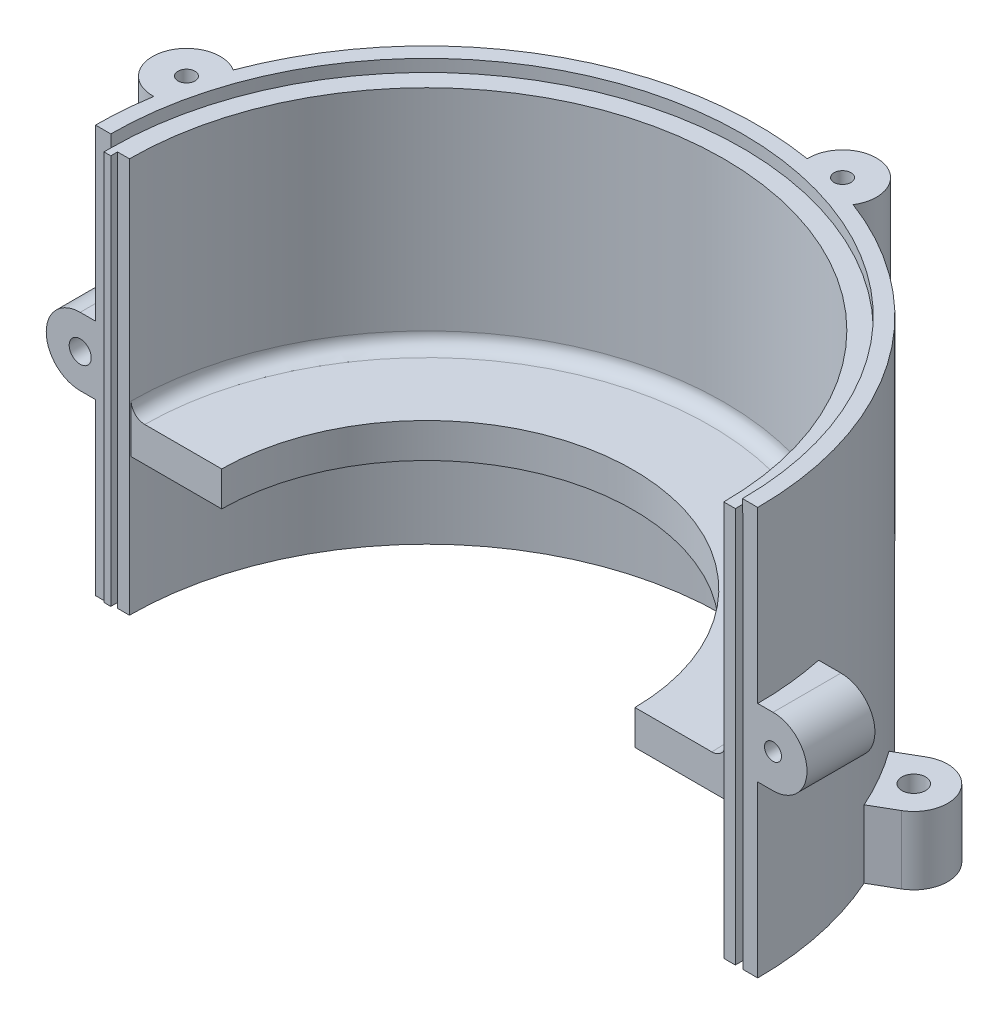
SolidWorks part; units mm, degrees
ref_plane "Plano frontal" through (0, 0, 0) normal (0, 0, 1) x (1, 0, 0)
ref_plane "Plano superior" through (0, 0, 0) normal (0, 1, 0) x (1, 0, 0)
ref_plane "Plano direito" through (0, 0, 0) normal (1, 0, 0) x (0, 0, -1)
sketch "Esboço3" plane through (0, 0, 0) normal (0, 0, 1) x (1, 0, 0)
  line L2 (97.5, 79.8) -> (97.5, 11.3045)
  line L4 (87.5, 0) -> (60.3424, 0)
  line L6 (60.3424, 0) -> (60.3424, 10.2)
  line L18 (97.5, 79.8) -> (93, 79.8)
  line L19 (93, 79.8) -> (93, 76.2)
  line L20 (93, 76.2) -> (87.5, 76.2)
  line L21 (87.5, 76.2) -> (87.5, 14.2)
  line L22 (83.5, 10.2) -> (60.3424, 10.2)
  line L30 (55, 0) -> (-55, 0) construction
  line L33 (97.5, 0) -> (97.5, 11.3045)
  line L34 (97.5, 0) -> (97.5, -40.2)
  line L35 (97.5, -40.2) -> (87.5, -40.2)
  line L36 (87.5, -40.2) -> (87.5, 0)
  arc A1 (87.5, 14.2) -> (83.5, 10.2) centre (83.5, 14.2) cw
  dimension "D32" = 79.8
  dimension "D5" = 120
  dimension "D11" = 66
  dimension "D12" = 3.6
  dimension "D13" = 93
  dimension "D14" = 10
  dimension "D18" = 10
  dimension "D30" = 23.1576
  dimension "D31" = 97.5
  dimension "D33" = 37.1576
ref_axis "Eixo1" through (0, -3.3221, 0) along (0, 1, 0)
revolve "Revolução2" add sketch "Esboço3" angle 180 about axis through (0, -3.3221, 0) along (0, 1, 0)
sketch "Esboço20" [suppressed] plane through (0, 0, 0) normal (0, 0, 1) x (1, 0, 0)
  line L0 (60.3424, 2.95) -> (60.3424, 10.2)
  line L1 (83.5, 10.2) -> (-83.5, 10.2) construction
  line L2 (60.3424, 10.2) -> (55.5, 10.2)
  line L3 (83.5, 10.2) -> (55.5, 10.2) construction
  line L4 (55.5, 10.2) -> (38.8, 26.9)
  line L5 (38.8, 26.9) -> (38.8, 44.96)
  line L6 (38.8, 44.96) -> (32.3, 44.96) construction
  line L7 (38.8, 44.96) -> (32.3, 44.96)
  line L8 (32.3, 44.96) -> (-32.3, 44.96) construction
  line L9 (32.3, 44.96) -> (31.3, 43.96)
  line L10 (31.3, 43.96) -> (31.3, 25.96)
  line L11 (31.3, 25.96) -> (27.6265, 25.96)
  line L12 (31.3, 25.96) -> (-31.3, 25.96) construction
  line L13 (27.6265, 25.96) -> (19.3, 21.2) construction
  line L14 (27.6265, 25.96) -> (19.3, 21.2)
  line L15 (19.3, 21.2) -> (19.3, 21.05)
  line L16 (19.3, 21.05) -> (15.3, 21.05)
  line L17 (15.3, 21.05) -> (15.3, 17.7)
  line L18 (15.3, 17.7) -> (19.3, 17.7)
  line L19 (19.3, 17.7) -> (19.3, 17)
  line L20 (19.3, 17) -> (22.6, 17)
  line L21 (22.6, 17) -> (22.6, 13.7)
  line L22 (22.6, 13.7) -> (31, 13.7)
  line L23 (31, 13.7) -> (31, 10.95)
  line L24 (31, 10.95) -> (44, 10.95)
  line L25 (44, 10.95) -> (52, 2.95)
  line L26 (52, 2.95) -> (60.3424, 2.95)
revolve "Revolução3" [suppressed] add sketch "Esboço20" angle 360 about axis through (0, -3.3221, 0) along (0, 1, 0)
sketch "Esboço4" plane through (0, 79.8, 0) normal (0, 1, 0) x (1, 0, 0)
  line L0 (25.8817, 96.5917) -> (-96.5917, 25.8817) construction
  line L1 (-96.5917, 25.8817) -> (-25.8817, -96.5917) construction
  line L2 (-25.8817, -96.5917) -> (96.5917, -25.8817) construction
  line L3 (96.5917, -25.8817) -> (25.8817, 96.5917) construction
  line L6 (0, 0) -> (25.8817, 96.5917) construction
  line L7 (96.5917, -25.8817) -> (0, 0) construction
  line L8 (0, 0) -> (-96.5917, 25.8817) construction
  line L9 (-25.8817, -96.5917) -> (0, 0) construction
  line L10 (0, 0) -> (0, 126.0952) construction
  circle A0 centre (25.8817, 96.5917) radius 10
  circle A3 centre (-96.5917, 25.8817) radius 10
  dimension "D2" = 20
  dimension "D1" = 141.42
  dimension "D3" = 15
extrude "Ressalto-extrusão1" add sketch "Esboço4" against normal blind 35
sketch "Esboço5" plane through (0, -40.2, 0) normal (0, -1, 0) x (1, 0, 0)
  line L0 (0, 0) -> (25.8817, -96.5917) construction
  line L1 (0, 0) -> (0, -105) construction
  line L2 (10, -105) -> (10, -96.9858)
  line L3 (-10, -105) -> (-10, -96.9858)
  line L4 (10, -96.9858) -> (-10, -96.9858)
  arc A1 (10, -105) -> (-10, -105) centre (0, -105) cw
  arc A3 (-97.5, 0) -> (97.5, 0) centre (0, 0) ccw construction
  dimension "D2" = 10
  dimension "D1" = 105
extrude "Ressalto-extrusão2" add sketch "Esboço5" against normal blind 20
sketch "Esboço8" plane through (0, -40.2, 0) normal (0, -1, 0) x (1, 0, 0)
  circle A0 centre (0, -105) radius 3.5
  dimension "D1" = 7
extrude "Corte-extrusão2" cut sketch "Esboço8" against normal blind 20
pattern_circular "PadrãoCircular1" count 6 over 360 about axis through (0, 0, 0) along (0, 1, 0) of "Ressalto-extrusão2", "Corte-extrusão2"
sketch "Esboço6" plane through (0, 79.8, 0) normal (0, 1, 0) x (1, 0, 0)
  circle A2 centre (25.8817, 96.5917) radius 2.5
  circle A3 centre (-96.5917, 25.8817) radius 2.5
  dimension "D1" = 5
extrude "Corte-extrusão1" cut sketch "Esboço6" against normal blind 15
sketch "Esboço9" [suppressed] plane through (0, 13.7, 0) normal (0, -1, 0) x (1, 0, 0)
  line L0 (0, 0) -> (18.7383, -18.7383) construction
  line L1 (-18.7383, -18.7383) -> (0, 0) construction
  line L2 (-18.7383, -18.7383) -> (18.7383, -18.7383) construction
  circle A2 centre (18.7383, -18.7383) radius 1.25
  circle A3 centre (-18.7383, -18.7383) radius 1.25
  point P13 (4.0879, -3.0957)
  dimension "D2" = 26.5
  dimension "D1" = 26.5
extrude "Corte-extrusão3" [suppressed] cut sketch "Esboço9" against normal blind 6
sketch "Esboço10" plane through (0, 0, 0) normal (0, 0, 1) x (1, 0, 0)
  line L0 (93.1, -40.2) -> (93.1, 76.2)
  line L1 (93, 76.2) -> (93.1, 76.2) construction
  line L2 (90.9, 76.2) -> (91, 76.2) construction
  line L3 (93.1, 76.2) -> (90.9, 76.2)
  line L5 (90.9, 76.2) -> (90.9, -40.2)
  line L6 (90.9, -40.2) -> (93.1, -40.2)
  line L7 (87.5, -40.2) -> (97.5, -40.2) construction
  dimension "D1" = 2
  dimension "D2" = 0.1
extrude "Corte-extrusão4" cut sketch "Esboço10" against normal blind 3.5
sketch "Esboço11" plane through (0, 0, 0) normal (0, 0, 1) x (1, 0, 0)
  line L0 (-91, -38.7) -> (-91, 76.2)
  line L1 (-87.5, -40.2) -> (-97.5, -40.2) construction
  line L3 (-91, 76.2) -> (-93, 76.2)
  line L4 (-93, 76.2) -> (-93, -38.7)
  line L5 (-93, -38.7) -> (-91, -38.7)
  line L6 (-93, 79.8) -> (-93, 76.2) construction
  line L7 (-93, 76.2) -> (-87.5, 76.2) construction
  dimension "D1" = 2
  dimension "D2" = 1.5
extrude "Ressalto-extrusão5" add sketch "Esboço11" along normal blind 2
sketch "Esboço12" plane through (0, 0, 0) normal (0, 0, 1) x (1, 0, 0)
  line L0 (-124.1305, 19.8) -> (136.9824, 19.8) construction
  line L1 (-97.5, -40.2) -> (-97.5, 79.8) construction
  line L2 (-97.5, -40.2) -> (-97.5, 79.8) construction
  line L3 (-102, 9.8) -> (-102, 29.8) construction
  line L4 (-102, 29.8) -> (-87.5, 29.8)
  line L5 (-87.5, 76.2) -> (-87.5, 14.2) construction
  line L6 (-87.5, 29.8) -> (-87.5, 9.8)
  line L7 (-87.5, 9.8) -> (-102, 9.8)
  arc A1 (-102, 9.8) -> (-102, 29.8) centre (-102, 19.8) cw
  circle A2 centre (-102, 19.8) radius 3.25
  point P8 (-97.5, 19.8)
  dimension "D2" = 6.5
  dimension "D1" = 20
  dimension "D3" = 4.5
extrude "Ressalto-extrusão6" add sketch "Esboço12" against normal blind 20
sketch "Esboço13" plane through (0, 0, 0) normal (0, 0, 1) x (1, 0, 0)
  line L0 (102, 29.8) -> (102, 9.8) construction
  line L3 (-102, 19.8) -> (140.3594, 19.8) construction
  line L4 (102, 29.8) -> (93.1, 29.8)
  line L5 (93.1, 29.8) -> (93.1, 9.8)
  line L6 (93.1, 9.8) -> (102, 9.8)
  line L7 (93.1, -40.2) -> (93.1, 76.2) construction
  line L8 (97.5, -40.2) -> (97.5, 79.8) construction
  arc A0 (102, 9.8) -> (102, 29.8) centre (102, 19.8) ccw
  circle A1 centre (102, 19.8) radius 2.5
  dimension "D3" = 5
  dimension "D1" = 20
  dimension "D2" = 4.5
extrude "Ressalto-extrusão7" add sketch "Esboço13" against normal blind 20
sketch "Esboço14" [suppressed] plane through (0, 0, 0) normal (0, -1, 0) x (-1, 0, 0)
  line L0 (0, -185) -> (0, 115) construction
  arc A0 (32.1753, 52.6546) -> (-32.1753, 52.6546) centre (0, -166.8724) ccw construction
  arc A1 (34.3505, 67.4961) -> (-34.3505, 67.4961) centre (0, -166.8724) ccw
  arc A2 (30, 37.8132) -> (-30, 37.8132) centre (0, -166.8724) ccw
  arc A3 (30, 37.8132) -> (34.3505, 67.4961) centre (32.1753, 52.6546) ccw
  arc A4 (-34.3505, 67.4961) -> (-30, 37.8132) centre (-32.1753, 52.6546) ccw
  arc A5 (10, 105) -> (-10, 105) centre (0, 105) ccw construction
  point P3 (0, 55)
  dimension "D1" = 30
  dimension "D2" = 300
  dimension "D3" = 55
  dimension "D4" = 60
extrude "Corte-extrusão5" [suppressed] cut sketch "Esboço14" against normal through all
sketch "Esboço16" plane through (0, 76.2, 0) normal (0, 1, 0) x (1, 0, 0)
  circle A0 centre (0, 0) radius 93
extrude "Corte-extrusão6" cut sketch "Esboço16" along normal blind 10
sketch "Esboço17" plane through (0, -40.2, 0) normal (0, -1, 0) x (1, 0, 0)
  circle A0 centre (0, 0) radius 92.9674
  circle A1 centre (0, 0) radius 90.9674
  dimension "D1" = 2
extrude "Corte-extrusão7" cut sketch "Esboço17" against normal blind 1.5
ref_plane "Plano1" [suppressed] through (0, -20.1, 0) normal (0, -1, 0) x (-1, 0, 0)
sketch "Esboço18" [suppressed] plane through (0, -20.1, 0) normal (0, -1, 0) x (-1, 0, 0)
  line L0 (0, 0) -> (0, 115) construction
  line L1 (50, 81.2817) -> (-50, 81.2817)
  line L2 (50, 81.2817) -> (50, 64.043)
  line L3 (50, 64.043) -> (-50, 64.043)
  line L4 (-50, 81.2817) -> (-50, 64.043)
  line L5 (50, 81.2817) -> (-50, 64.043) construction
  line L6 (50, 64.043) -> (-50, 81.2817) construction
  arc A0 (10, 105) -> (-10, 105) centre (0, 105) ccw construction
  point P0 (0, 72.6623)
  dimension "D1" = 100
extrude "Corte-extrusão8" [suppressed] cut sketch "Esboço18" against normal mid plane 30
sketch "Esboço19" [suppressed] plane through (0, -20.1, 0) normal (0, -1, 0) x (-1, 0, 0)
  line L0 (32.3966, 81.2817) -> (-32.3966, 81.2817)
  arc A0 (32.3966, 81.2817) -> (-32.3966, 81.2817) centre (0, 0) ccw
  arc A1 (87.5, 0) -> (-87.5, 0) centre (0, 0) ccw construction
extrude "Ressalto-extrusão9" [suppressed] add sketch "Esboço19" along normal mid plane 30
sketch "Esboço21" plane through (0, 0, 0) normal (0, -1, 0) x (1, 0, 0)
  line L0 (-87.5, 0) -> (87.5, 0)
  line L1 (-60.8404, -0.5) -> (-87.4986, -0.5)
  line L2 (60.8404, -0.5) -> (87.4986, -0.5)
  line L3 (0, -60.8424) -> (0, -60.3424) construction
  line L4 (-60.8404, -0.5) -> (-60.8404, 0) construction
  arc A0 (-87.5, 0) -> (-87.4986, -0.5) centre (0, 0) ccw
  arc A1 (87.5, 0) -> (87.4986, -0.5) centre (0, 0) cw
  arc A2 (-60.8404, -0.5) -> (60.8404, -0.5) centre (0, 0) ccw
  arc A4 (-60.3424, 0) -> (60.3424, 0) centre (0, 0) ccw construction
  dimension "D1" = 0.5
extrude "Corte-extrusão9" cut sketch "Esboço21" against normal through all both and the other way through all
